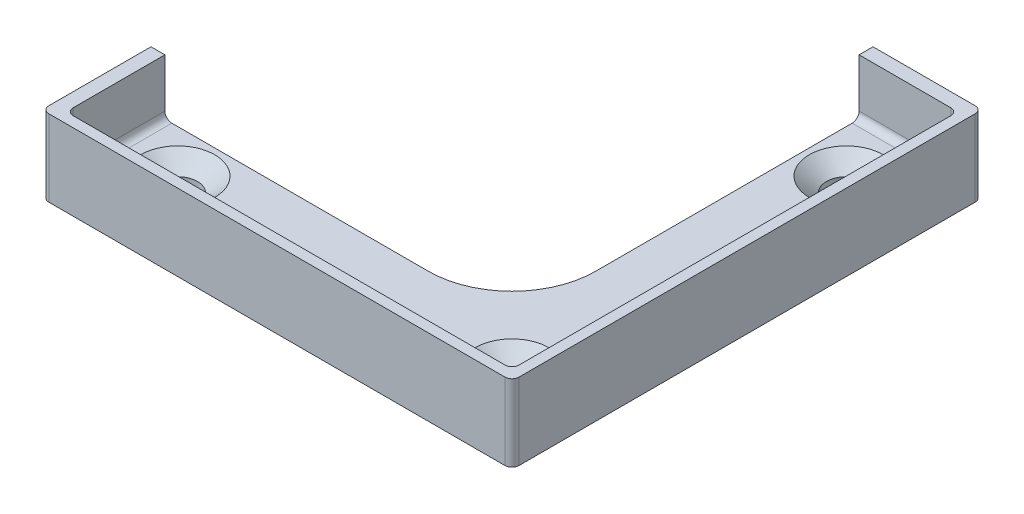
SolidWorks part; units mm, degrees
ref_plane "Front Plane" through (0, 0, 0) normal (0, 0, 1) x (1, 0, 0)
ref_plane "Top Plane" through (0, 0, 0) normal (0, 1, 0) x (1, 0, 0)
ref_plane "Right Plane" through (0, 0, 0) normal (1, 0, 0) x (0, 0, -1)
sketch "Sketch1" plane through (0, 0, 0) normal (0, 1, 0) x (1, 0, 0)
  line L0 (0, 25.4) -> (0, 26.9875) construction
  line L1 (-25.4, 25.4) -> (25.4, 25.4)
  line L2 (-25.4, 25.4) -> (-25.4, -25.4)
  line L3 (-25.4, -25.4) -> (25.4, -25.4)
  line L4 (25.4, 25.4) -> (25.4, -25.4)
  line L5 (-25.4, 25.4) -> (25.4, -25.4) construction
  line L6 (-25.4, -25.4) -> (25.4, 25.4) construction
  line L7 (-26.9875, 26.9875) -> (26.9875, 26.9875)
  line L8 (-26.9875, 26.9875) -> (-26.9875, -26.9875)
  line L9 (-26.9875, -26.9875) -> (26.9875, -26.9875)
  line L10 (26.9875, 26.9875) -> (26.9875, -26.9875)
  line L11 (-26.9875, 26.9875) -> (26.9875, -26.9875) construction
  line L12 (-26.9875, -26.9875) -> (26.9875, 26.9875) construction
  line L13 (-26.9875, 0) -> (-25.4, 0) construction
  point P0 (0, 0)
  point P6 (0, 0)
  dimension "D1" = 1.5875
  dimension "D2" = 50.8
extrude "Boss-Extrude1" add sketch "Sketch1" along normal blind 6.35
sketch "Sketch2" plane through (0, 0, 0) normal (0, -1, 0) x (1, 0, 0)
  line L4 (26.9875, -26.9875) -> (26.9875, 26.9875)
  line L5 (26.9875, 26.9875) -> (-26.9875, 26.9875)
  line L6 (-26.9875, 26.9875) -> (-26.9875, -26.9875)
  line L7 (-26.9875, -26.9875) -> (26.9875, -26.9875)
  line L8 (26.9875, -26.9875) -> (26.9875, 26.9875)
  line L9 (26.9875, 26.9875) -> (-26.9875, 26.9875)
  line L10 (-26.9875, 26.9875) -> (-26.9875, -26.9875)
  line L11 (-26.9875, -26.9875) -> (26.9875, -26.9875)
  dimension "D1" = 0
extrude "Boss-Extrude2" add sketch "Sketch2" along normal blind 2.3813
sketch "Sketch3" plane through (0, -2.3813, 0) normal (0, -1, 0) x (1, 0, 0)
  line L0 (-26.9875, 26.5906) -> (26.5906, 26.5906)
  line L1 (26.5906, 26.5906) -> (26.5906, -26.9875)
  line L3 (26.5906, -26.9875) -> (28.1781, -26.9875)
  line L4 (28.1781, -26.9875) -> (28.1781, 28.1781)
  line L5 (28.1781, 28.1781) -> (-26.9875, 28.1781)
  line L6 (-26.9875, 28.1781) -> (-26.9875, 26.5906)
  line L7 (-26.9875, -26.9875) -> (26.9875, -26.9875) construction
  line L8 (-26.9875, 26.9875) -> (-26.9875, -26.9875) construction
  line L9 (26.9875, -26.9875) -> (26.9875, 26.9875) construction
  dimension "D1" = 1.5875
  dimension "D2" = 0.3969
extrude "Boss-Extrude3" add sketch "Sketch3" along normal blind 3.2512 and the other way blind 1.5875
fillet "Fillet1" [suppressed] radius 0.5953
sketch "Sketch4" plane through (0, 0, 0) normal (0, 1, 0) x (1, 0, 0)
  line L0 (25.4, -25.4) -> (19.05, -19.05) construction
  line L1 (-25.4, 25.4) -> (-19.05, 19.05) construction
  line L2 (25.4, -25.4) -> (25.4, 25.4) construction
  line L3 (-25.4, 25.4) -> (-25.4, -25.4) construction
  line L4 (-25.4, 25.4) -> (-25.4, -25.4) construction
  line L5 (-19.05, 19.05) -> (19.05, 19.05)
  line L6 (-19.05, 19.05) -> (-19.05, -19.05)
  line L7 (-19.05, -19.05) -> (19.05, -19.05)
  line L8 (19.05, 19.05) -> (19.05, -19.05)
  point P2 (19.4015, 19.4015)
  point P6 (-19.05, -19.05)
  point P7 (19.05, -19.05)
  point P8 (-19.05, 19.05)
  point P9 (-19.4015, -19.4015)
  point P19 (19.05, 19.05)
  dimension "D1" = 6.35
hole_wizard "CSK for #8 Flat Head Machine Screw (100)1" positions "3DSketch1" profile "Sketch5" countersink size "#8" standard "ANSI Inch" end condition through all
sketch3d "3DSketch1"
  point P0 (19.05, 0, 19.05)
  point P3 (-19.05, 0, -19.05)
  point P6 (19.05, 0, -19.05)
  point P9 (-19.05, 0, 19.05)
sketch "Sketch5" plane through (19.05, 0, 19.05) normal (1, 0, 0) x (0, 0, 1)
  line L0 (0, 0) -> (0, 5.6324)
  line L1 (0, 5.6324) -> (2.2479, 5.6324)
  line L2 (2.2479, 5.6324) -> (2.2479, 1.6518)
  line L3 (2.2479, 1.6518) -> (4.2164, 0)
  line L5 (4.2164, 0) -> (0, 0)
  line L6 (-2.2479, 1.6518) -> (-4.2164, 0) construction
  line L11 (0, -6.35) -> (0, 107.95) construction
  dimension "Thru Hole Dia." = 4.4958
  dimension "Thru Hole Depth" = 5.6325
  dimension "Near C'Sink Dia." = 8.4328
  dimension "Near C'Sink Angle" = 100
sketch "Sketch6" plane through (0, 0, 0) normal (0, 1, 0) x (1, 0, 0)
  circle A0 centre (19.05, -19.05) radius 4.8895 construction
sketch "Sketch7" plane through (0, 0, 0) normal (0, 1, 0) x (1, 0, 0)
  line L0 (-26.9875, 26.9875) -> (-26.9875, -26.9875) construction
  line L1 (-26.9875, -14.1605) -> (14.1605, -14.1605)
  line L2 (-26.9875, -14.1605) -> (-26.9875, 26.9875)
  line L3 (-26.9875, 26.9875) -> (14.1605, 26.9875)
  line L4 (14.1605, -14.1605) -> (14.1605, 26.9875)
  line L5 (26.9875, 26.9875) -> (-26.9875, 26.9875) construction
  line L6 (25.4, -25.4) -> (19.05, -19.05) construction
  line L7 (19.05, -19.05) -> (14.1605, -14.1605) construction
  circle A2 centre (19.05, -19.05) radius 4.8895 construction
  point P8 (13.8146, -12.7667)
  point P13 (13.4031, -13.4031)
  point P14 (14.512, -14.512)
extrude "Cut-Extrude1" cut sketch "Sketch7" against normal through all both and the other way through all
fillet "Fillet2" radius 9.525 1 edges at (14.1605, -1.1906, 14.1605)
sketch "Sketch8" plane through (0, -0.7938, 0) normal (0, 1, 0) x (1, 0, 0)
  line L6 (28.1781, 26.9875) -> (26.9875, 26.9875)
  line L7 (26.9875, 26.9875) -> (26.9875, -26.9875)
  line L8 (26.9875, -26.9875) -> (-26.9875, -26.9875)
  line L9 (-26.9875, -26.9875) -> (-26.9875, -28.1781)
  line L10 (-26.9875, -28.1781) -> (28.1781, -28.1781)
  line L11 (28.1781, -28.1781) -> (28.1781, 26.9875)
  line L12 (28.1781, 26.9875) -> (26.9875, 26.9875)
  line L13 (26.9875, 26.9875) -> (26.9875, -26.9875)
  line L14 (26.9875, -26.9875) -> (-26.9875, -26.9875)
  line L15 (-26.9875, -26.9875) -> (-26.9875, -28.1781)
  line L16 (-26.9875, -28.1781) -> (28.1781, -28.1781)
  line L17 (28.1781, -28.1781) -> (28.1781, 26.9875)
  dimension "D1" = 0
extrude "Boss-Extrude4" add sketch "Sketch8" along normal up to surface (7.1437 mm away) up to face at (2.8321, 6.35, 2.8321)
sketch "Sketch9" plane through (0, -5.6325, 0) normal (0, -1, 0) x (1, 0, 0)
  line L6 (-26.9875, 28.1781) -> (-26.9875, 26.5906)
  line L7 (-26.9875, 26.5906) -> (26.5906, 26.5906)
  line L8 (26.5906, 26.5906) -> (26.5906, -26.9875)
  line L9 (26.5906, -26.9875) -> (28.1781, -26.9875)
  line L10 (28.1781, -26.9875) -> (28.1781, 28.1781)
  line L11 (28.1781, 28.1781) -> (-26.9875, 28.1781)
  line L12 (-26.9875, 28.1781) -> (-26.9875, 26.5906)
  line L13 (-26.9875, 26.5906) -> (26.5906, 26.5906)
  line L14 (26.5906, 26.5906) -> (26.5906, -26.9875)
  line L15 (26.5906, -26.9875) -> (28.1781, -26.9875)
  line L16 (28.1781, -26.9875) -> (28.1781, 28.1781)
  line L17 (28.1781, 28.1781) -> (-26.9875, 28.1781)
  dimension "D1" = 0
extrude "Cut-Extrude2" cut sketch "Sketch9" against normal through all
fillet "Fillet3" radius 0.7937 10 edges at (26.5906, 1.9844, -26.9875) (26.5906, 1.9844, 26.5906) (-26.9875, 1.9844, 26.5906) (19.7803, 0, -25.4) (25.4, 3.175, -25.4) (25.4, 0, 0) (25.4, 3.175, 25.4) (-25.4, 0, 19.7802) (-25.4, 3.175, 25.4) (0, 0, 25.4)
